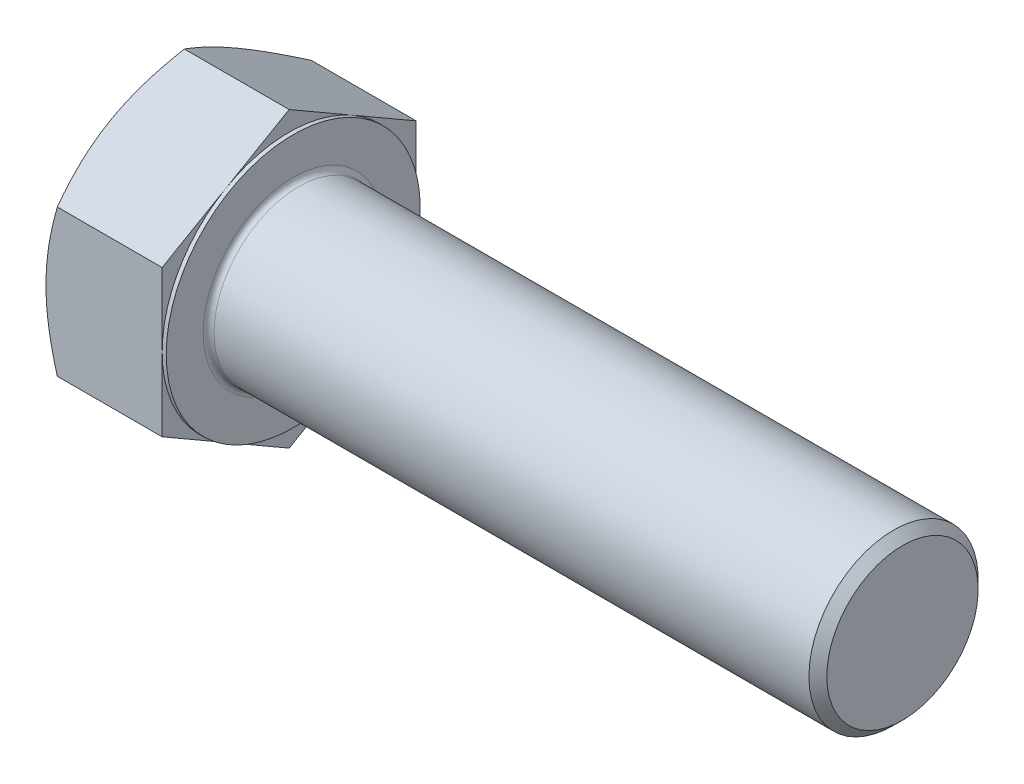
SolidWorks part; units mm, degrees
extrude "BaseHead" add sketch "Sketch1" along normal blind 11.2776
sketch "Sketch1" plane through (0, 0, 0) normal (1, 0, 0) x (0, 0, -1)
  line L0 (11.9126, 6.8777) -> (11.9126, -6.8777)
  line L1 (-11.9126, 6.8777) -> (-11.9126, -6.8777)
  line L2 (11.9126, -6.8777) -> (0, -13.7555)
  line L3 (0, -13.7555) -> (-11.9126, -6.8777)
  line L4 (11.9126, 6.8777) -> (0, 13.7555)
  line L5 (0, 13.7555) -> (-11.9126, 6.8777)
  dimension "Width_flats" = 23.8252
  dimension "D2" = 120
  dimension "D3" = 11.9126
  dimension "D4" = 11.9126
  dimension "D5" = 11.9126
revolve "HeadChamfer" cut sketch "Sketch3" angle 360 about L6
sketch "Sketch3" plane through (0, 0, 0) normal (0, 0, 1) x (1, 0, 0)
  line L0 (0, 11.9126) -> (4.7302, 20.1055)
  line L1 (0, 13.7555) -> (0, 6.8777) construction
  line L2 (4.7302, 20.1055) -> (4.7302, 26.4555)
  line L3 (4.7302, 26.4555) -> (-12.7, 26.4555)
  line L4 (-12.7, 26.4555) -> (-12.7, 11.9126)
  line L5 (-12.7, 11.9126) -> (0, 11.9126)
  line L6 (0, 0) -> (99.06, 0) construction
  line L7 (11.2776, 13.7555) -> (0, 13.7555) construction
  dimension "D1" = 11.9126
  dimension "D2" = 6.35
  dimension "D3" = 12.7
  dimension "D4" = 6.35
  dimension "Head_ch_ang" = 30
material "AISI 1020 Steel, Cold Rolled"
ref_plane "Plane1" through (0, 0, 0) normal (0, 0, 1) x (1, 0, 0)
ref_plane "Plane2" through (0, 0, 0) normal (0, 1, 0) x (1, 0, 0)
ref_plane "Plane3" through (0, 0, 0) normal (1, 0, 0) x (0, 0, -1)
sketch "BodySke" plane through (0, 0, 0) normal (0, 0, 1) x (1, 0, 0)
  line L0 (0, 6.8777) -> (0, -6.8777) construction
  line L1 (0, 0) -> (68.4276, 0)
  line L2 (0, 0) -> (0, 7.9375)
  line L3 (0, 7.9375) -> (67.5881, 7.9375)
  line L4 (68.4276, 0) -> (68.4276, 7.098)
  line L5 (11.2776, 13.7555) -> (11.2776, 6.8777) construction
  line L6 (68.4276, 7.098) -> (67.5881, 7.9375)
  line L7 (0, 0) -> (96.52, 0) construction
  line L8 (68.4276, -7.098) -> (67.5881, -7.9375) construction
  line L9 (0, -7.9375) -> (67.5881, -7.9375) construction
  line L10 (12.6873, 15.24) -> (12.6873, -1.27) construction
  line L11 (11.2776, 15.24) -> (11.2776, -1.27) construction
  line L12 (11.2776, 6.8777) -> (11.2776, -6.8777) construction
  dimension "Diameter" = 15.875
revolve "BaseBody" add sketch "BodySke" angle 360 about L7
cosmetic thread "ThreadCosmetic" [suppressed]
sketch "Sketch4" plane through (0, 0, 0) normal (0, 0, 1) x (1, 0, 0)
  line L1 (11.2776, 13.7555) -> (11.2776, 6.8777) construction
  line L2 (11.2776, 11.9126) -> (10.8966, 11.9126)
  line L3 (11.2776, 11.9126) -> (11.2776, 39.1555)
  line L4 (11.2776, 39.1555) -> (10.8966, 39.1555)
  line L5 (0, 0) -> (95.25, 0) construction
  line L6 (0, 0) -> (96.52, 0) construction
  line L7 (10.8966, 11.9126) -> (10.8966, 39.1555)
  line L8 (11.2776, 13.7555) -> (1.064, 13.7555) construction
  dimension "D1" = 11.9126
  dimension "D2" = 25.4
revolve "BearingFace" cut sketch "Sketch4" angle 360 about L5
fillet "HeadFillet" radius 0.508 1 edges at (11.2776, 0, -7.9375)
sketch "ThdSchSke" plane through (0, 0, 0) normal (0, 0, 1) x (1, 0, 0)
  line L0 (12.6873, -7.098) -> (12.0995, -7.9375)
  line L1 (12.6873, -7.098) -> (13.2751, -7.9375)
  line L2 (13.2751, -7.9375) -> (13.2751, -9.9219)
  line L3 (-3.175, 0) -> (5.1513, 0) construction
  line L5 (13.2751, -9.9219) -> (12.0995, -9.9219)
  line L6 (12.0995, -9.9219) -> (12.0995, -7.9375)
  dimension "Thread_minor" = 14.1961
  dimension "Diameter" = 15.875
  dimension "Start" = 12.6873
revolve "ThreadSchematic" [suppressed] cut sketch "ThdSchSke" angle 360 about L3
pattern_linear "ThdSchPat" [suppressed]
equation "\"D3@Sketch1\" = \"Width_flats@Sketch1\" / 2"
equation "\"D4@Sketch1\" = \"D3@Sketch1\""
equation "\"D5@Sketch1\" = \"D4@Sketch1\""
equation "\"Thread_minor@ThreadCosmetic\" = \"Minor_dia@BodySke\""
equation "\"D1@Sketch3\" = \"Width_flats@Sketch1\" / 2"
equation "\"D1@Sketch4\"= \"Width_flats@Sketch1\" / 2"
equation "\"Thread_length@ThreadCosmetic\"= ((sgn( (\"Length@BodySke\" - \"Advance@BodySke\" ) - \"Thread_nom@BodySke\" )-1)*( (\"Length@BodySke\" - \"Advance@BodySke\" ) - \"Thread_nom@BodySke\" ))/-2+ \"Thread_nom@BodySke\""
equation "\"Thread_minor@ThdSchSke\"= \"Minor_dia@BodySke\""
equation "\"Diameter@ThdSchSke\" = \"Diameter@BodySke\""
equation "\"Overcut@ThdSchSke\" = \"Diameter@BodySke\" * 1.25"
equation "\"Start@ThdSchSke\" = \"Head_ht@BaseHead\" + \"Length@BodySke\" - \"Thread_length@ThreadCosmetic\"  '---Non-countersunk---"
equation "\"Num_threads@ThdSchPat\" = int( \"Thread_length@ThreadCosmetic\" / \"Advance@BodySke\" + 0.999 )  + 1"
equation "\"Advance@ThdSchPat\" = \"Thread_length@ThreadCosmetic\" /  (\"Num_threads@ThdSchPat\" - 1) 'relax it"
equation "\"Num_threads@ThdSchPat\" = \"Num_threads@ThdSchPat\" - sgn( \"Num_threads@ThdSchPat\" - 1) '---chamfered tips only---"
